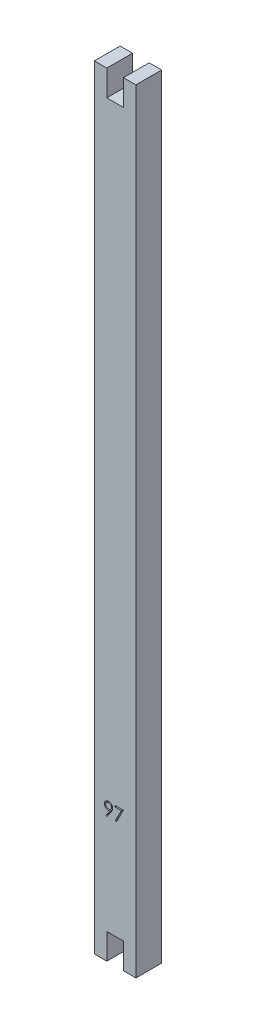
SolidWorks part; units mm, degrees
ref_plane "Front Plane" through (0, 0, 0) normal (0, 0, 1) x (1, 0, 0)
ref_plane "Top Plane" through (0, 0, 0) normal (0, 1, 0) x (1, 0, 0)
ref_plane "Right Plane" through (0, 0, 0) normal (1, 0, 0) x (0, 0, -1)
sketch "Sketch2" plane through (0, 0, 0) normal (0, 0, 1) x (1, 0, 0)
  line L0 (0, 0) -> (0, 186.19)
  line L2 (10, 186.19) -> (10, 0)
  line L3 (10, 0) -> (7, 0)
  line L4 (3, 0) -> (3, 6.2)
  line L5 (3, 6.2) -> (7, 6.2)
  line L6 (7, 6.2) -> (7, 0)
  line L11 (3, 0) -> (0, 0)
  line L12 (3, 186.19) -> (3, 179.99)
  line L13 (3, 179.99) -> (7, 179.99)
  line L14 (7, 179.99) -> (7, 186.19)
  line L15 (0, 186.19) -> (3, 186.19)
  line L16 (7, 186.19) -> (10, 186.19)
  dimension "D1" = 173.79
  dimension "D2" = 10
  dimension "D3" = 4
  dimension "D4" = 3
  dimension "D5" = 6.2
  dimension "D6" = 6.2
extrude "Boss-Extrude1" add sketch "Sketch2" along normal blind 6.2
sketch "Sketch3" plane through (0, 0, 6.2) normal (0, 0, 1) x (1, 0, 0)
  text T0 "97"
extrude "Cut-Extrude1" cut sketch "Sketch3" against normal blind 1
